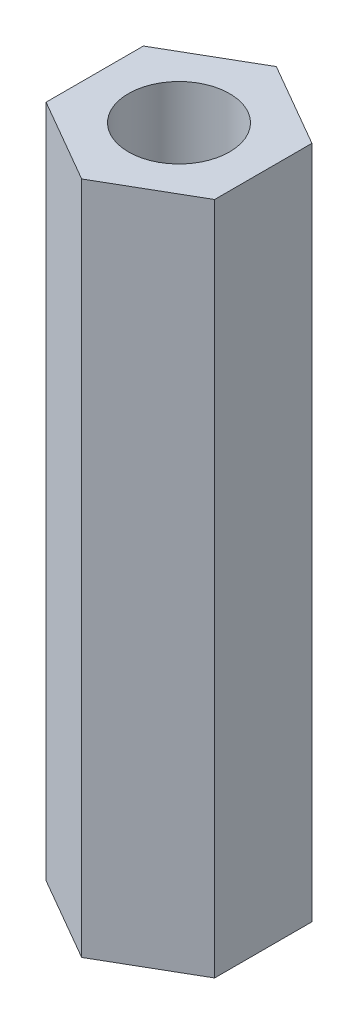
SolidWorks part; units mm, degrees
ref_plane "Front Plane" through (0, 0, 0) normal (0, 0, 1) x (1, 0, 0)
ref_plane "Top Plane" through (0, 0, 0) normal (0, 1, 0) x (1, 0, 0)
ref_plane "Right Plane" through (0, 0, 0) normal (1, 0, 0) x (0, 0, -1)
sketch "Sketch1" plane through (0, 0, 0) normal (0, 1, 0) x (1, 0, 0)
  line L1 (0, -5.7735) -> (5, -2.8868)
  line L2 (5, -2.8868) -> (5, 2.8868)
  line L3 (5, 2.8868) -> (0, 5.7735)
  line L4 (0, 5.7735) -> (-5, 2.8868)
  line L5 (-5, 2.8868) -> (-5, -2.8868)
  line L6 (-5, -2.8868) -> (0, -5.7735)
  circle A0 centre (0, 0) radius 5 construction
  dimension "D1" = 10
extrude "Boss-Extrude1" add sketch "Sketch1" along normal blind 40
sketch "Sketch3" plane through (0, 0, 0) normal (0, -1, 0) x (1, 0, 0)
  circle A0 centre (0, 0) radius 3
  dimension "D1" = 6
extrude "Cut-Extrude1" cut sketch "Sketch3" against normal blind 12
sketch "Sketch4" plane through (0, 40, 0) normal (0, 1, 0) x (1, 0, 0)
  circle A0 centre (0, 0) radius 3 construction
  circle A1 centre (0, 0) radius 3
extrude "Cut-Extrude2" cut sketch "Sketch4" against normal blind 12
